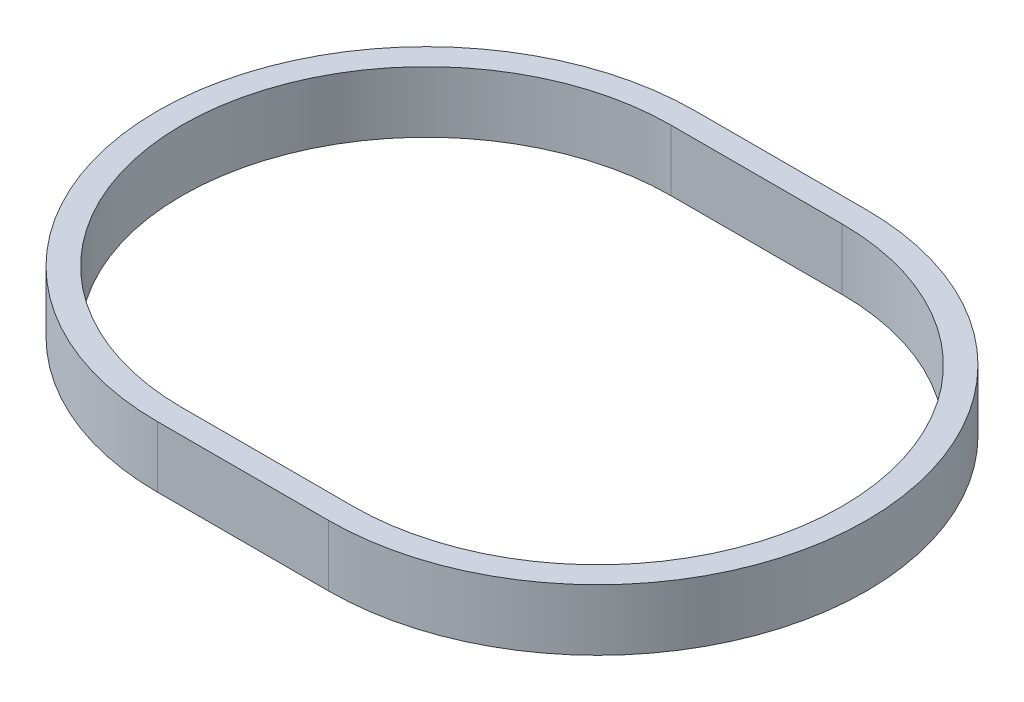
SolidWorks part; units mm, degrees
ref_plane "Front Plane" through (0, 0, 0) normal (0, 0, 1) x (1, 0, 0)
ref_plane "Top Plane" through (0, 0, 0) normal (0, 1, 0) x (1, 0, 0)
ref_plane "Right Plane" through (0, 0, 0) normal (1, 0, 0) x (0, 0, -1)
sketch "Sketch1" plane through (0, 0, 0) normal (0, 1, 0) x (1, 0, 0)
  line L0 (0, 20) -> (14, 20)
  line L1 (0, -20) -> (14, -20)
  line L2 (0, 22) -> (14, 22)
  line L3 (0, -22) -> (14, -22)
  arc A0 (0, 20) -> (0, -20) centre (0, 0) ccw
  arc A1 (14, -20) -> (14, 20) centre (14, 0) ccw
  arc A2 (14, -22) -> (14, 22) centre (14, 0) ccw
  arc A3 (0, 22) -> (0, -22) centre (0, 0) ccw
  dimension "D1" = 20
  dimension "D2" = 20
  dimension "D3" = 14
  dimension "D4" = 2
extrude "Boss-Extrude1" add sketch "Sketch1" along normal blind 5
